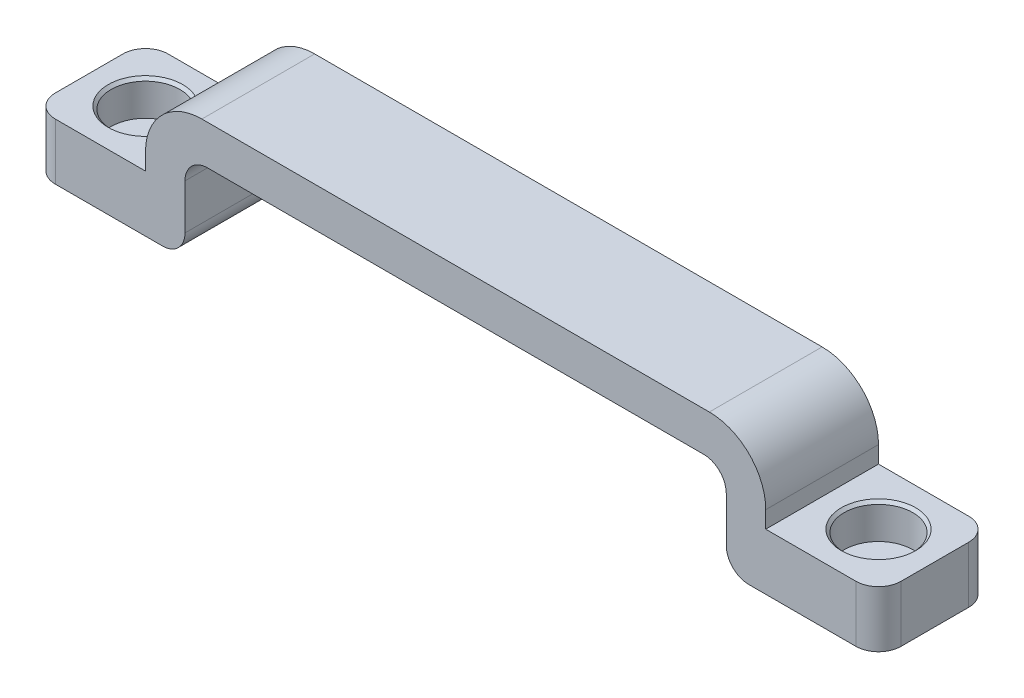
SolidWorks part; units mm, degrees
ref_plane "Front Plane" through (0, 0, 0) normal (0, 0, 1) x (1, 0, 0)
ref_plane "Top Plane" through (0, 0, 0) normal (0, 1, 0) x (1, 0, 0)
ref_plane "Right Plane" through (0, 0, 0) normal (1, 0, 0) x (0, 0, -1)
sketch "Sketch1" plane through (0, 0, 0) normal (0, 0, 1) x (1, 0, 0)
  line L0 (-27.5, 3.5) -> (27.5, 3.5)
  line L1 (27.5, 3.5) -> (27.5, -3)
  line L2 (27.5, -8) -> (24, -8)
  line L3 (24, -8) -> (24, 0)
  line L8 (0, 0) -> (0, 16.5989) construction
  line L9 (-24, 0) -> (24, 0)
  line L10 (27.5, -3) -> (37.5, -3)
  line L12 (27.5, -8) -> (37.5, -8)
  line L13 (37.5, -3) -> (37.5, -8)
  line L14 (32.5, -3) -> (32.5, -8) construction
  line L15 (-32.5, -3) -> (-32.5, -8) construction
  line L16 (-37.5, -3) -> (-37.5, -8)
  line L17 (-27.5, -8) -> (-37.5, -8)
  line L18 (-27.5, -3) -> (-37.5, -3)
  line L19 (-24, -8) -> (-24, 0)
  line L20 (-27.5, -8) -> (-24, -8)
  line L21 (-27.5, 3.5) -> (-27.5, -3)
  point P22 (0, 3.5)
  dimension "D5" = 3.5
  dimension "D6" = 5
  dimension "D7" = 10
  dimension "D1" = 3.5
  dimension "D2" = 65
  dimension "D3" = 8
extrude "Boss-Extrude1" add sketch "Sketch1" along normal mid plane 10
sketch "Sketch3" plane through (0, -3, 0) normal (0, 1, 0) x (1, 0, 0)
  line L0 (37.5, 0) -> (27.5, 0) construction
  line L1 (37.5, -5) -> (37.5, 5) construction
  line L2 (27.5, -5) -> (27.5, 5) construction
  line L3 (-37.5, 0) -> (-27.5, 0) construction
  line L4 (-37.5, -5) -> (-37.5, 5) construction
  line L5 (-27.5, -5) -> (-27.5, 5) construction
  circle A0 centre (32.5, 0) radius 3.05
  circle A1 centre (-32.5, 0) radius 3.05
  point P12 (-32.5, 0)
  point P13 (32.5, 0)
  dimension "D1" = 6.1
fillet "Fillet1" radius 2 2 edges at (24, 0, 0) (-24, 0, 0)
fillet "Fillet2" radius 5 2 edges at (-27.5, 3.5, 0) (27.5, 3.5, 0)
fillet "Fillet3" radius 2 4 edges at (-37.5, -5.5, -5) (-37.5, -5.5, 5) (37.5, -5.5, -5) (37.5, -5.5, 5)
fillet "Fillet4" radius 2 2 edges at (-24, -8, 0) (24, -8, 0)
extrude "Cut-Extrude1" cut sketch "Sketch3" against normal blind 3.1
chamfer "Chamfer1" distance 0.25 angle 45 2 edges at (-35.55, -3, 0) (29.45, -3, 0)
equation "\"D1@Sketch1\"=\"D5@Sketch1\""
